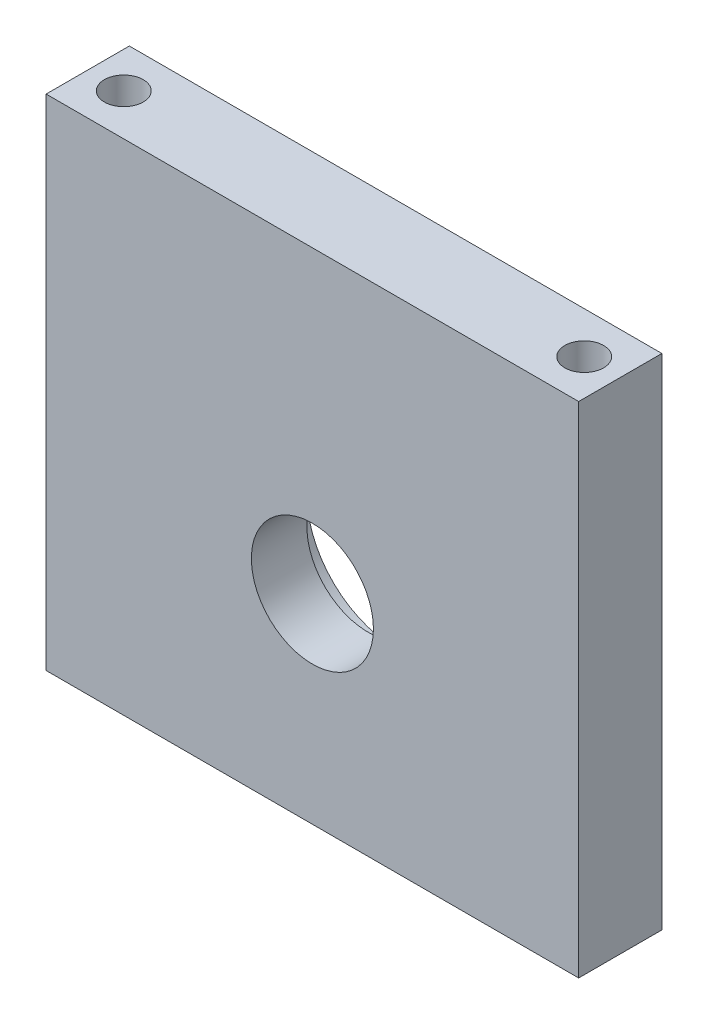
SolidWorks part; units mm, degrees
ref_plane "Plan de face" through (0, 0, 0) normal (0, 0, 1) x (1, 0, 0)
ref_plane "Plan de dessus" through (0, 0, 0) normal (0, 1, 0) x (1, 0, 0)
ref_plane "Plan de droite" through (0, 0, 0) normal (1, 0, 0) x (0, 0, -1)
sketch "Esquisse1" plane through (0, 0, 0) normal (0, 0, 1) x (1, 0, 0)
  line L1 (-24, 22.5) -> (24, 22.5)
  line L2 (-24, 22.5) -> (-24, -22.5)
  line L3 (-24, -22.5) -> (24, -22.5)
  line L4 (24, 22.5) -> (24, -22.5)
  line L5 (-24, 22.5) -> (24, -22.5) construction
  line L6 (-24, -22.5) -> (24, 22.5) construction
  point P0 (0, 0)
  dimension "D1" = 45
  dimension "D2" = 48
extrude "Boss.-Extru.1" add sketch "Esquisse1" along normal blind 7.5
sketch "Esquisse2" plane through (0, -22.5, 0) normal (0, -1, 0) x (1, 0, 0)
  line L0 (-24, 3.75) -> (24, 3.75) construction
  line L3 (-24, 7.5) -> (-24, 0) construction
  line L4 (24, 7.5) -> (24, 0) construction
  line L5 (-20.75, 5.5) -> (-20.75, 7.5) construction
  line L6 (-24, 7.5) -> (24, 7.5) construction
  line L7 (-22.5, 3.75) -> (-24, 3.75) construction
  line L8 (22.5, 3.75) -> (24, 3.75) construction
  circle A0 centre (-20.75, 3.75) radius 1.75
  circle A1 centre (20.75, 3.75) radius 1.75
  dimension "D1" = 3.5
  dimension "D2" = 3.5
  dimension "D3" = 41.5
  dimension "D4" = 1.5
extrude "Enlèv. mat.-Extru.1" cut sketch "Esquisse2" against normal blind 7
sketch "Esquisse3" plane through (0, 22.5, 0) normal (0, 1, 0) x (1, 0, 0)
  line L0 (-24, -3.75) -> (24, -3.75) construction
  line L1 (-24, -7.5) -> (-24, 0) construction
  line L2 (24, -7.5) -> (24, 0) construction
  line L3 (-22.5, -3.75) -> (-24, -3.75) construction
  line L4 (22.5, -3.75) -> (24, -3.75) construction
  circle A0 centre (-20.75, -3.75) radius 1.75
  circle A1 centre (20.75, -3.75) radius 1.75
  dimension "D3" = 3.5
  dimension "D4" = 3.5
  dimension "D1" = 41.5
  dimension "D2" = 1.5
extrude "Enlèv. mat.-Extru.2" cut sketch "Esquisse3" against normal blind 7
sketch "Esquisse4" plane through (0, 0, 0) normal (0, 0, -1) x (-1, 0, 0)
  line L0 (24, -22.5) -> (-24, -22.5) construction
  line L1 (0, 22.5) -> (0, -22.5) construction
  line L2 (-24, 22.5) -> (24, 22.5) construction
  circle A0 centre (0, -4.5) radius 8
  point P8 (0, 0)
  dimension "D1" = 18
  dimension "D2" = 16
sketch "Esquisse5" plane through (0, 0, 7.5) normal (0, 0, 1) x (1, 0, 0)
  circle A0 centre (0, -4.5) radius 5.5
  dimension "D1" = 11
extrude "Enlèv. mat.-Extru.3" cut sketch "Esquisse5" against normal blind 5
extrude "Enlèv. mat.-Extru.4" cut sketch "Esquisse4" against normal blind 2.5
